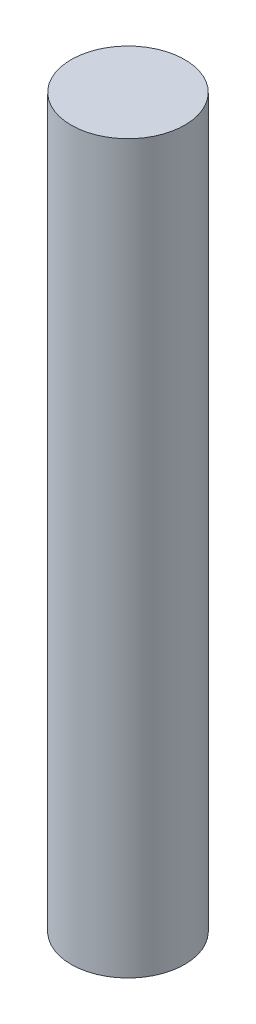
SolidWorks part; units mm, degrees
ref_plane "Alzado" through (0, 0, 0) normal (0, 0, 1) x (1, 0, 0)
ref_plane "Planta" through (0, 0, 0) normal (0, 1, 0) x (1, 0, 0)
ref_plane "Vista lateral" through (0, 0, 0) normal (1, 0, 0) x (0, 0, -1)
sketch "Croquis1" plane through (0, 0, 0) normal (0, 1, 0) x (1, 0, 0)
  circle A0 centre (0, 0) radius 0.5
  dimension "D1" = 1
extrude "Saliente-Extruir1" add sketch "Croquis1" along normal blind 6.4
